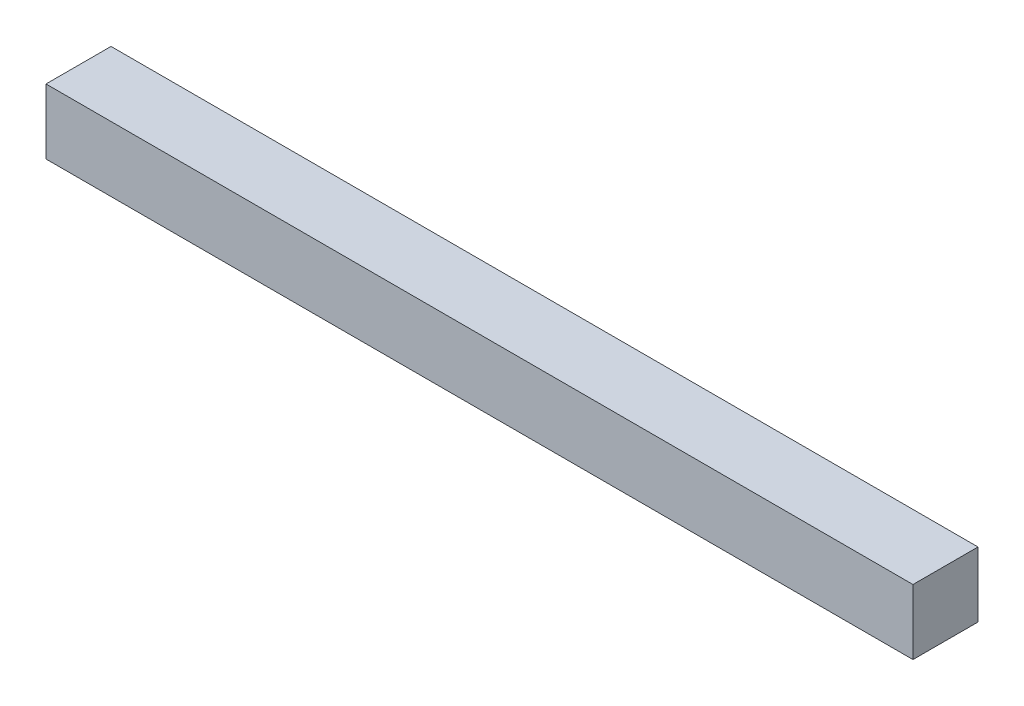
SolidWorks part; units mm, degrees
material "Plain Carbon Steel"
ref_plane "Front Plane" through (0, 0, 0) normal (0, 0, 1) x (1, 0, 0)
ref_plane "Top Plane" through (0, 0, 0) normal (0, 1, 0) x (1, 0, 0)
ref_plane "Right Plane" through (0, 0, 0) normal (1, 0, 0) x (0, 0, -1)
sketch "Sketch1" plane through (0, 0, 0) normal (1, 0, 0) x (0, 0, -1)
  line L1 (-2.3812, 2.3813) -> (2.3813, 2.3813)
  line L2 (-2.3812, 2.3813) -> (-2.3812, -2.3812)
  line L3 (-2.3812, -2.3812) -> (2.3813, -2.3812)
  line L4 (2.3813, 2.3813) -> (2.3813, -2.3812)
  line L5 (-2.3812, 2.3813) -> (2.3813, -2.3812) construction
  line L6 (-2.3812, -2.3812) -> (2.3813, 2.3813) construction
  point P0 (0, 0)
  dimension "D1" = 4.7625
  dimension "D2" = 4.7625
extrude "Boss-Extrude1" add sketch "Sketch1" along normal blind 63.5
